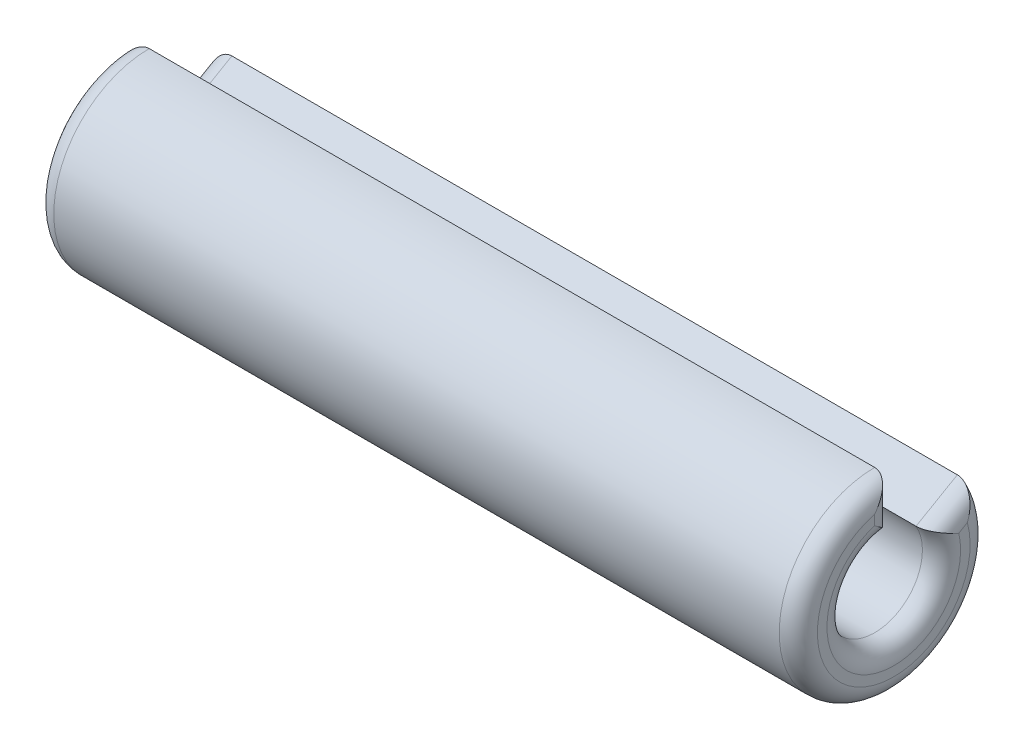
SolidWorks part; units mm, degrees
material "Plain Carbon Steel"
ref_plane "Front Plane" through (0, 0, 0) normal (0, 0, 1) x (1, 0, 0)
ref_plane "Top Plane" through (0, 0, 0) normal (0, 1, 0) x (1, 0, 0)
ref_plane "Right Plane" through (0, 0, 0) normal (1, 0, 0) x (0, 0, -1)
sketch "Sketch1" plane through (0, 0, 0) normal (0, 0, 1) x (1, 0, 0)
  line L0 (0, 0) -> (2, 0) construction
  line L1 (-2, 0.5) -> (2, 0.5)
  line L2 (-2, 0.5) -> (-2, 0.25)
  line L3 (-2, 0.25) -> (2, 0.25)
  line L4 (2, 0.5) -> (2, 0.25)
  line L5 (0, 0) -> (0, 0.5) construction
  dimension "D1" = 1
  dimension "D2" = 4
  dimension "D3" = 0.25
revolve "Revolve1" add sketch "Sketch1" angle 300 about L0
fillet "Fillet1" radius 0.1 8 edges at (-2, 0.375, 0) (-2, -0.433, 0.25) (-2, 0.1875, -0.3248) (-2, -0.2165, 0.125) (2, 0.375, 0) (2, -0.2165, 0.125) (2, 0.1875, -0.3248) (2, -0.433, 0.25)
